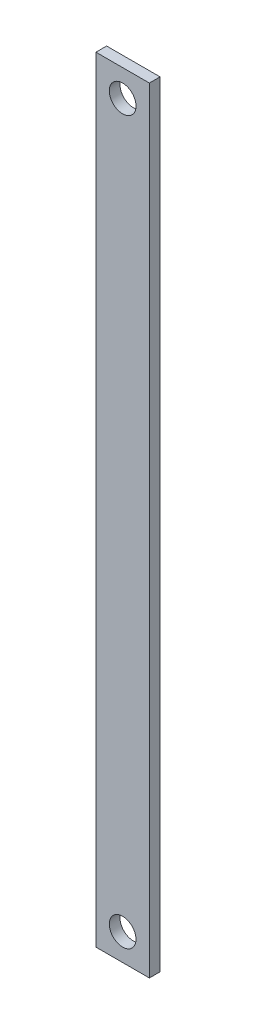
SolidWorks part; units mm, degrees
ref_plane "Спереди" through (0, 0, 0) normal (0, 0, 1) x (1, 0, 0)
ref_plane "Сверху" through (0, 0, 0) normal (0, 1, 0) x (1, 0, 0)
ref_plane "Справа" through (0, 0, 0) normal (1, 0, 0) x (0, 0, -1)
sketch "Эскиз1" plane through (0, 0, 0) normal (0, 1, 0) x (1, 0, 0)
  line L1 (0, 0) -> (20, 0)
  line L2 (0, 0) -> (0, 4)
  line L3 (0, 4) -> (20, 4)
  line L4 (20, 0) -> (20, 4)
extrude "Бобышка-Вытянуть1" add sketch "Эскиз1" along normal blind 290
sketch "Эскиз2" plane through (0, 0, 0) normal (0, 0, 1) x (1, 0, 0)
  line L0 (0, 145) -> (27.928, 145) construction
  line L1 (0, 290) -> (0, 0) construction
  circle A0 centre (10, 10) radius 5
  circle A1 centre (10, 280) radius 5
extrude "Вырез-Вытянуть1" cut sketch "Эскиз2" against normal through all
